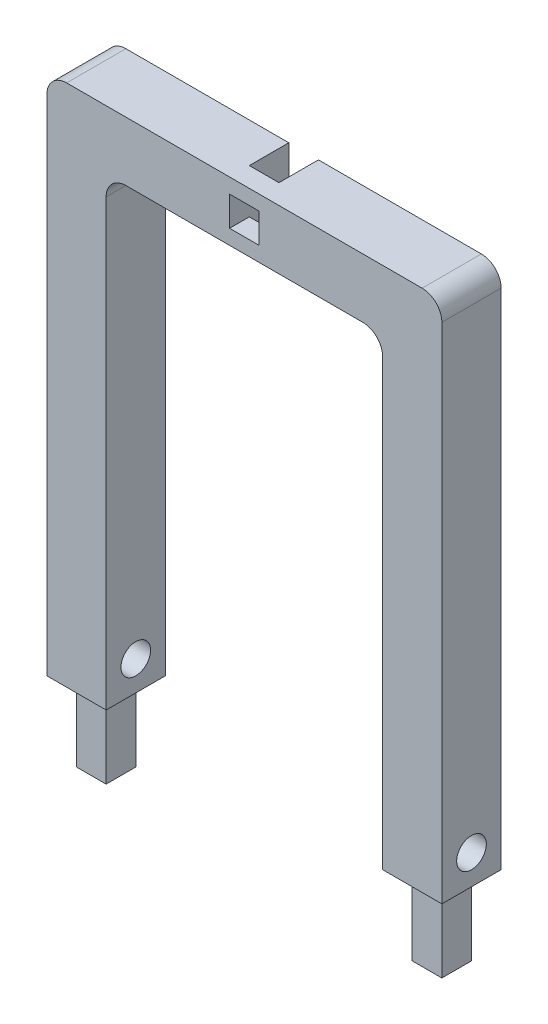
SolidWorks part; units mm, degrees
ref_plane "Front Plane" through (0, 0, 0) normal (0, 0, 1) x (1, 0, 0)
ref_plane "Top Plane" through (0, 0, 0) normal (0, 1, 0) x (1, 0, 0)
ref_plane "Right Plane" through (0, 0, 0) normal (1, 0, 0) x (0, 0, -1)
sketch "Sketch1" plane through (0, 0, 0) normal (0, 0, 1) x (1, 0, 0)
  line L0 (-77.931, -87.8818) -> (-107.931, -87.8818)
  line L1 (-107.931, -87.8818) -> (-107.931, 177.1182)
  line L2 (-107.931, 177.1182) -> (92.069, 177.1182)
  line L3 (92.069, 177.1182) -> (92.069, -87.8818)
  line L4 (92.069, -87.8818) -> (62.069, -87.8818)
  line L5 (62.069, -87.8818) -> (62.069, 147.1182)
  line L6 (62.069, 147.1182) -> (-77.931, 147.1182)
  line L7 (-77.931, 147.1182) -> (-77.931, -87.8818)
  line L8 (0, 0) -> (0, 235) construction
  dimension "D1" = 140
  dimension "D2" = 265
  dimension "D3" = 30
  dimension "D4" = 30
extrude "Boss-Extrude1" add sketch "Sketch1" along normal blind 30
sketch "Sketch2" plane through (0, -87.8818, 0) normal (0, -1, 0) x (1, 0, 0)
  line L0 (62.069, 0) -> (92.069, 0) construction
  line L1 (69.569, 22.5) -> (84.569, 22.5)
  line L2 (69.569, 22.5) -> (69.569, 7.5)
  line L3 (69.569, 7.5) -> (84.569, 7.5)
  line L4 (84.569, 22.5) -> (84.569, 7.5)
  line L5 (92.069, 30) -> (92.069, 0) construction
  line L6 (-77.931, 30) -> (-77.931, 0) construction
  line L8 (-100.431, 22.5) -> (-85.431, 22.5)
  line L9 (-100.431, 22.5) -> (-100.431, 7.5)
  line L10 (-100.431, 7.5) -> (-85.431, 7.5)
  line L11 (-85.431, 22.5) -> (-85.431, 7.5)
  point P0 (77.802, 15.1361)
  point P7 (-93.4326, 16.6198)
  dimension "D1" = 7.5
  dimension "D2" = 7.5
  dimension "D3" = 15
  dimension "D4" = 7.5
extrude "Boss-Extrude2" add sketch "Sketch2" along normal blind 40
fillet "Fillet1" radius 10 2 edges at (62.069, 147.1182, 15) (-77.931, 147.1182, 15)
fillet "Fillet2" radius 10 2 edges at (-107.931, 177.1182, 15) (92.069, 177.1182, 15)
sketch "Sketch3" plane through (-77.931, 0, 0) normal (1, 0, 0) x (0, 0, -1)
  line L0 (-30, -87.8818) -> (-30, 137.1182) construction
  line L2 (-30, -87.8818) -> (0, -87.8818) construction
  circle A0 centre (-15, -72.8818) radius 7.5
  dimension "D1" = 15
  dimension "D2" = 15
  dimension "D3" = 15
extrude "Cut-Extrude1" cut sketch "Sketch3" against normal through all both and the other way through all
sketch "Sketch4" plane through (0, 0, 0) normal (0, 0, -1) x (-1, 0, 0)
  line L1 (0.4309, 147.1182) -> (15.4309, 147.1182)
  line L2 (0.4309, 147.1182) -> (0.4309, 177.1182)
  line L3 (0.4309, 177.1182) -> (15.4309, 177.1182)
  line L4 (15.4309, 147.1182) -> (15.4309, 177.1182)
  line L6 (67.931, 147.1182) -> (-52.069, 147.1182) construction
  line L10 (-82.069, 177.1182) -> (97.931, 177.1182) construction
  dimension "D1" = 15
extrude "Cut-Extrude2" cut sketch "Sketch4" against normal blind 20
sketch "Sketch5" plane through (0, 0, 30) normal (0, 0, 1) x (1, 0, 0)
  line L0 (-15.4309, 147.1182) -> (-15.4309, 177.1182) construction
  line L1 (-15.4309, 169.6182) -> (-0.4309, 169.6182)
  line L2 (-15.4309, 169.6182) -> (-15.4309, 154.6182)
  line L3 (-15.4309, 154.6182) -> (-0.4309, 154.6182)
  line L4 (-0.4309, 169.6182) -> (-0.4309, 154.6182)
  line L5 (-0.4309, 177.1182) -> (-0.4309, 147.1182) construction
  line L6 (82.069, 177.1182) -> (-97.931, 177.1182) construction
  line L7 (-67.931, 147.1182) -> (52.069, 147.1182) construction
  dimension "D1" = 7.5
  dimension "D2" = 7.5
extrude "Cut-Extrude3" cut sketch "Sketch5" against normal blind 10
